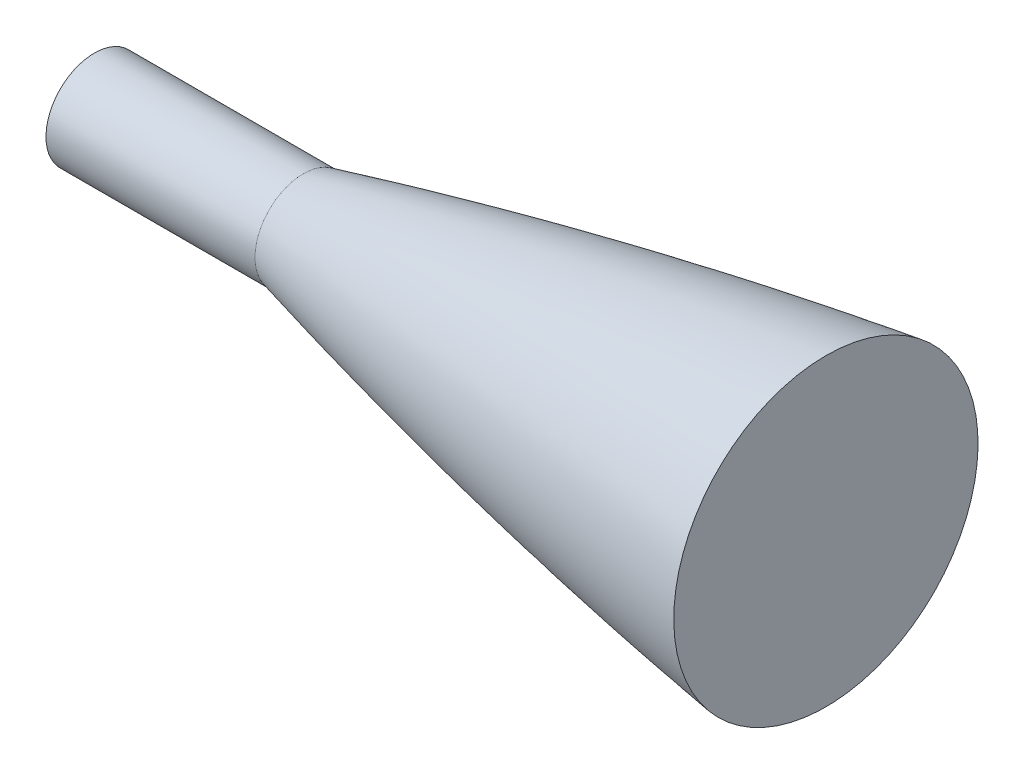
SolidWorks part; units mm, degrees
ref_plane "Front Plane" through (0, 0, 0) normal (0, 0, 1) x (1, 0, 0)
ref_plane "Top Plane" through (0, 0, 0) normal (0, 1, 0) x (1, 0, 0)
ref_plane "Right Plane" through (0, 0, 0) normal (1, 0, 0) x (0, 0, -1)
sketch "Sketch1" plane through (0, 0, 0) normal (0, 0, 1) x (1, 0, 0)
  line L0 (304.8, 49.784) -> (304.8, 0)
  line L1 (304.8, 0) -> (0, 0)
  line L2 (0, 0) -> (0, 11.7484)
  spline S0 degree 4 poles (-29.5658, 3.8633) (-28.9441, 4.0374) (-27.7007, 4.3845) (-25.2159, 5.0746) (-22.1117, 5.9273) (-19.0277, 6.7655) (-15.9353, 7.5966) (-13.5064, 8.2445) (-11.0138, 8.9031) (-8.6496, 9.5239) (-6.017, 10.2074) (-3.9348, 10.7459) (-0.8664, 11.529) (0.5497, 11.8883) (3.0854, 12.5273) (5.1062, 13.0323) (7.1101, 13.5293) (9.1599, 14.0344) (11.1954, 14.5321) (13.2334, 15.0269) (15.805, 15.6465) (18.9103, 16.3873) (22.5507, 17.2447) (26.7272, 18.2131) (31.9522, 19.4057) (42.4129, 21.7425) (62.3339, 25.9764) (110.7705, 35.2251) (160.7073, 42.1599) (207.7023, 46.435) (245.168, 48.3682) (253.7348, 48.741) (260.1614, 48.9835) (264.4463, 49.1304) (268.7317, 49.2625) (273.0175, 49.3798) (277.3037, 49.4823) (281.5902, 49.5699) (285.3296, 49.6334) (288.5217, 49.6785) (291.1667, 49.7098) (293.2638, 49.7311) (295.3592, 49.7488) (297.4702, 49.763) (299.5351, 49.7737) (301.6172, 49.7807) (304.2305, 49.7845) (305.6886, 49.7842) (308.8437, 49.7793) (310.9886, 49.769) (313.6963, 49.7536) (316.1321, 49.733) (318.7003, 49.7073) (321.2035, 49.6765) (323.7502, 49.6404) (326.2925, 49.5988) (328.8544, 49.5518) (331.4237, 49.4993) (333.3523, 49.4559) (334.6374, 49.4252) (335.2799, 49.4094) knots 0 0 0 0 0 0.006994 0.013988 0.027976 0.034844 0.041712 0.048579 0.055447 0.062315 0.069182 0.07605 0.082918 0.088602 0.094285 0.099969 0.105653 0.111336 0.11702 0.122704 0.128387 0.140005 0.151623 0.163241 0.174859 0.198094 0.267801 0.38398 0.709279 0.744133 0.778986 0.790604 0.802222 0.81384 0.825458 0.837075 0.848693 0.860311 0.871929 0.877613 0.883296 0.88898 0.894664 0.900347 0.906031 0.911715 0.917398 0.92424 0.931081 0.937923 0.944764 0.951606 0.958447 0.965289 0.97213 0.979098 0.986065 0.993033 1 1 1 1 1 construction
  spline S1 degree 4 poles (0, 11.7484) (0.4242, 11.8559) (1.2778, 12.0717) (3.0854, 12.5273) (5.1062, 13.0323) (7.1101, 13.5293) (9.1599, 14.0344) (11.1954, 14.5321) (13.2334, 15.0269) (15.805, 15.6465) (18.9103, 16.3873) (22.5507, 17.2447) (26.7272, 18.2131) (31.9522, 19.4057) (42.4129, 21.7425) (62.3339, 25.9764) (110.7705, 35.2251) (160.7073, 42.1599) (207.7023, 46.435) (245.168, 48.3682) (253.7348, 48.741) (260.1614, 48.9835) (264.4463, 49.1304) (268.7317, 49.2625) (273.0175, 49.3798) (277.3037, 49.4823) (281.5902, 49.5699) (285.3296, 49.6334) (288.5217, 49.6785) (291.1667, 49.7098) (293.2638, 49.7311) (295.3592, 49.7488) (297.4702, 49.763) (299.5351, 49.7737) (301.6172, 49.7807) (303.4822, 49.7834) (304.3624, 49.784) (304.8, 49.784) knots 0.082918 0.082918 0.082918 0.082918 0.082918 0.088602 0.094285 0.099969 0.105653 0.111336 0.11702 0.122704 0.128387 0.140005 0.151623 0.163241 0.174859 0.198094 0.267801 0.38398 0.709279 0.744133 0.778986 0.790604 0.802222 0.81384 0.825458 0.837075 0.848693 0.860311 0.871929 0.877613 0.883296 0.88898 0.894664 0.900347 0.906031 0.911715 0.917398 0.917398 0.917398 0.917398 0.917398
  dimension "D1" = 49.784
  dimension "D2" = 304.8
revolve "Revolve1" add sketch "Sketch1" angle 360 about L1
sketch "Sketch2" plane through (304.8, 0, 0) normal (1, 0, 0) x (0, 0, -1)
  circle A0 centre (0, 0) radius 49.784
extrude "Boss-Extrude1" add sketch "Sketch2" along normal blind 203.2
sketch "Sketch3" plane through (0, 0, 0) normal (-1, 0, 0) x (0, 0, 1)
  circle A0 centre (0, 0) radius 11.7484
extrude "Boss-Extrude2" add sketch "Sketch3" along normal blind 50.8
ref_plane "Plane1" through (127, 0, 0) normal (1, 0, 0) x (0, 0, -1)
sketch "Sketch4" plane through (127, 0, 0) normal (1, 0, 0) x (0, 0, -1)
  circle A0 centre (0, 0) radius 54.6045
extrude "Cut-Extrude1" cut sketch "Sketch4" along normal through all
